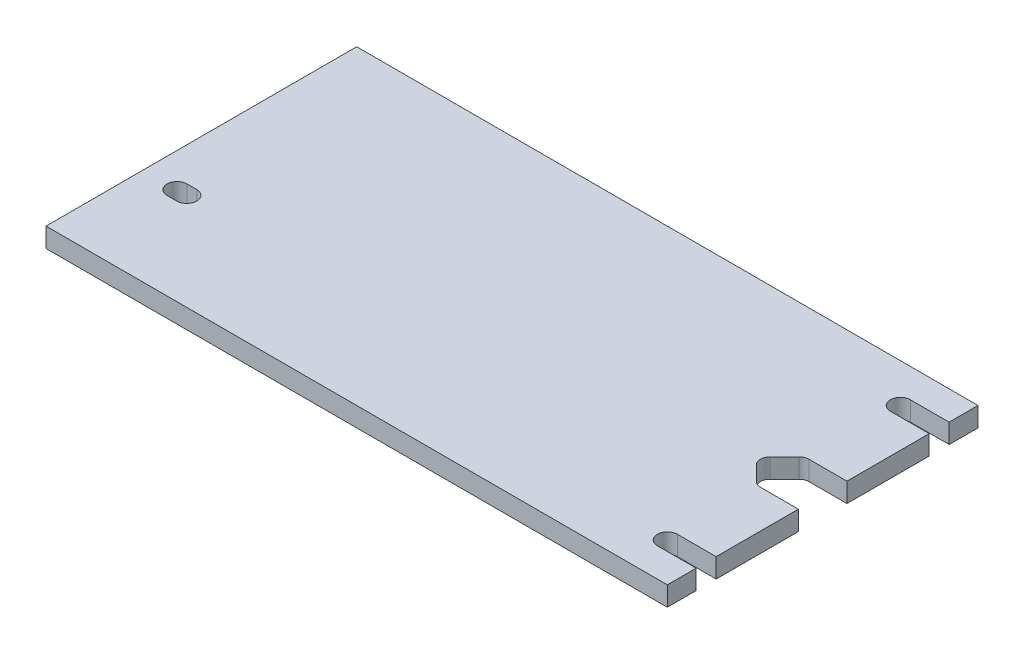
SolidWorks part; units mm, degrees
material "Acrylic (Medium-high impact)"
ref_plane "Front Plane" through (0, 0, 0) normal (0, 0, 1) x (1, 0, 0)
ref_plane "Top Plane" through (0, 0, 0) normal (0, 1, 0) x (1, 0, 0)
ref_plane "Right Plane" through (0, 0, 0) normal (1, 0, 0) x (0, 0, -1)
sketch "Sketch1" plane through (0, 0, 0) normal (0, 1, 0) x (1, 0, 0)
  line L0 (0, 11.3076) -> (0, -10.8315) construction
  line L1 (-101.6, 50.8) -> (101.6, 50.8)
  line L2 (-101.6, 50.8) -> (-101.6, -50.8)
  line L3 (-101.6, -50.8) -> (101.6, -50.8)
  line L4 (101.6, 50.8) -> (101.6, 7.9375)
  line L5 (-101.6, 50.8) -> (101.6, -50.8) construction
  line L6 (-101.6, -50.8) -> (101.6, 50.8) construction
  line L7 (-24.7577, 0) -> (22.1391, 0) construction
  line L8 (86.9273, 7.0076) -> (82.1648, 2.2451)
  line L9 (86.9273, -7.0076) -> (82.1648, -2.2451)
  line L10 (101.6, 0) -> (112.1126, 0) construction
  line L11 (101.6, -7.9375) -> (101.6, -50.8)
  line L12 (89.1724, 7.9375) -> (101.6, 7.9375)
  line L13 (89.1724, -7.9375) -> (101.6, -7.9375)
  circle A0 centre (-88.9, 38.1) radius 3.175 construction
  circle A1 centre (88.9, 38.1) radius 3.175 construction
  circle A2 centre (-88.9, -38.1) radius 3.175 construction
  circle A3 centre (88.9, -38.1) radius 3.175 construction
  circle A4 centre (88.9, 0) radius 3.175 construction
  circle A5 centre (88.9, 0) radius 6.35 construction
  arc A6 (82.1648, 2.2451) -> (82.1648, -2.2451) centre (84.4099, 0) ccw
  arc A7 (86.9273, -7.0076) -> (89.1724, -7.9375) centre (89.1724, -4.7625) ccw
  arc A8 (89.1724, 7.9375) -> (86.9273, 7.0076) centre (89.1724, 4.7625) ccw
  point P0 (0, 0)
  point P28 (79.9197, 0)
  point P33 (87.8572, -7.9375)
  point P36 (87.8572, 7.9375)
  dimension "D3" = 6.35
  dimension "D6" = 12.7
  dimension "D7" = 3.175
  dimension "D9" = 3.175
  dimension "D1" = 203.2
  dimension "D2" = 101.6
  dimension "D4" = 12.7
  dimension "D5" = 12.7
  dimension "D8" = 15.875
extrude "Boss-Extrude1" add sketch "Sketch1" along normal blind 6.35
hole_wizard "1/4 Clearance Hole1" positions "Sketch3" profile "Sketch2" hole size "1/4" standard "Ansi Inch" end condition up to next
sketch "Sketch3" plane through (0, 6.35, 0) normal (0, 1, 0) x (-1, 0, 0)
  line L0 (-101.6, -50.8) -> (101.6, -50.8) construction
  point P3 (-88.9, 38.1)
  point P6 (-88.9, -38.1)
  point P12 (88.9, 19.05)
  dimension "D1" = 69.85
sketch "Sketch2" plane through (88.9, 6.35, 38.1) normal (1, 0, 0) x (0, 0, 1)
  line L0 (0, 0) -> (0, 6.35)
  line L1 (0, 6.35) -> (3.2639, 6.35)
  line L2 (3.2639, 6.35) -> (3.2639, 0)
  line L5 (3.2639, 0) -> (0, 0)
  line L11 (0, -6.35) -> (0, 107.95) construction
  dimension "Thru Hole Dia." = 6.5278
  dimension "Thru Hole Depth" = 6.35
sketch "Sketch4" plane through (0, 6.35, 0) normal (0, 1, 0) x (1, 0, 0)
  line L0 (88.9, 41.3639) -> (101.6, 41.3639)
  line L1 (101.6, 7.9375) -> (101.6, 50.8) construction
  line L2 (88.9, 34.8361) -> (101.6, 34.8361)
  line L3 (101.6, 34.8361) -> (101.6, 41.3639)
  circle A0 centre (88.9, 38.1) radius 3.2639 construction
  arc A1 (88.9, 41.3639) -> (88.9, 34.8361) centre (88.9, 38.1) ccw
extrude "Cut-Extrude1" cut sketch "Sketch4" against normal up to next (6.35 mm away)
mirror "Mirror1" about plane through (0, 0, 0) normal (0, 0, 1) of "Cut-Extrude1"
sketch "Sketch5" plane through (0, 6.35, 0) normal (0, 1, 0) x (1, 0, 0)
  line L0 (-90.4875, -19.05) -> (-87.3125, -19.05) construction
  line L1 (-90.4875, -15.7861) -> (-87.3125, -15.7861)
  line L2 (-90.4875, -22.3139) -> (-87.3125, -22.3139)
  arc A0 (-90.4875, -15.7861) -> (-90.4875, -22.3139) centre (-90.4875, -19.05) ccw
  arc A1 (-87.3125, -22.3139) -> (-87.3125, -15.7861) centre (-87.3125, -19.05) ccw
  circle A3 centre (-88.9, -19.05) radius 3.2639 construction
  point P3 (-88.9, -19.05)
  dimension "D1" = 3.175
extrude "Cut-Extrude2" cut sketch "Sketch5" against normal up to next
